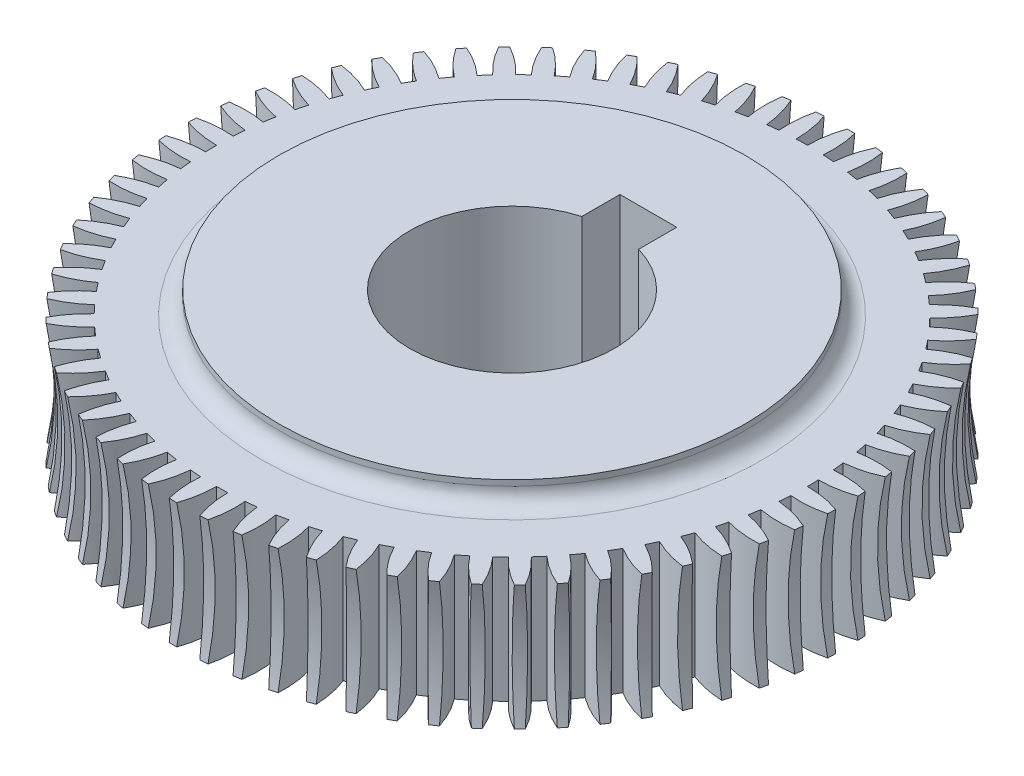
SolidWorks part; units mm, degrees
ref_plane "Front Plane" through (0, 0, 0) normal (0, 0, 1) x (1, 0, 0)
ref_plane "Top Plane" through (0, 0, 0) normal (0, 1, 0) x (1, 0, 0)
ref_plane "Right Plane" through (0, 0, 0) normal (1, 0, 0) x (0, 0, -1)
sketch "Sketch1" plane through (0, 0, 0) normal (0, 0, 1) x (1, 0, 0)
  line L5 (8.6582, -5.5) -> (37.6582, -5.5)
  line L7 (8.6582, 5.5) -> (37.6582, 5.5)
  line L9 (8.6582, 5.5) -> (8.6582, -5.5)
  arc A2 (37.6582, 5.5) -> (37.6582, -5.5) centre (67.1498, 0) ccw
  point P0 (0, 0)
  point P11 (8.6582, 0)
  dimension "D3" = 30
  dimension "D1" = 11
  dimension "D4" = 29
revolve "Revolve1" add sketch "Sketch1" angle 360 about L9
sketch "Sketch2" plane through (0, 5.5, 0) normal (0, 1, 0) x (1, 0, 0)
  circle A0 centre (8.6582, 0) radius 29 construction
  arc A3 (8.6582, -26) -> (9.6318, -25.9818) centre (8.6582, 0) ccw
  arc A4 (9.6318, -25.9818) -> (10.1451, -28.9619) centre (18.6318, -25.9659) ccw
  arc A5 (8.6582, -26) -> (8.1451, -28.9955) centre (-0.3418, -26) cw
  point P6 (9.1451, -25.9954)
  dimension "D1" = 52
  dimension "D3" = 9
  dimension "D4" = 9
  dimension "D7" = 3
  dimension "D2" = 1
  dimension "D5" = 2
  dimension "D6" = 1
extrude "Cut-Extrude1" cut sketch "Sketch2" against normal through all and the other way through all
pattern_circular "CirPattern1" count 68 over 360 about axis through (8.6582, 5.5, 0) along (0, 1, 0) of "Cut-Extrude1"
sketch "Sketch3" plane through (0, 5.5, 0) normal (0, 1, 0) x (1, 0, 0)
  line L1 (11.1582, 8.6458) -> (11.1582, 12)
  line L2 (6.1582, 8.6458) -> (6.1582, 12)
  line L6 (6.1582, 12) -> (11.1582, 12)
  arc A0 (31.7114, 12.023) -> (-14.3949, -12.023) centre (8.6582, 0) cw
  arc A1 (31.9325, 11.5892) -> (31.4822, 12.4526) centre (8.6582, 0) ccw construction
  arc A2 (-14.616, -11.5892) -> (-14.1657, -12.4526) centre (8.6582, 0) ccw construction
  circle A3 centre (8.6582, 0) radius 26
  arc A4 (6.1582, 8.6458) -> (11.1582, 8.6458) centre (8.6582, 0) ccw
  dimension "D1" = 18
extrude "Cut-Extrude2" cut sketch "Sketch3" against normal through all contours L2 A4 L1 L6
sketch "Sketch4" plane through (0, 5.5, 0) normal (0, 1, 0) x (1, 0, 0)
  line L0 (6.1582, 8.6458) -> (6.1582, 12)
  line L1 (6.1582, 12) -> (11.1582, 12)
  line L2 (11.1582, 12) -> (11.1582, 8.6458)
  circle A1 centre (8.6582, 0) radius 20.5
  arc A2 (6.1582, 8.6458) -> (11.1582, 8.6458) centre (8.6582, 0) ccw
  dimension "D1" = 41
extrude "Boss-Extrude1" add sketch "Sketch4" along normal blind 2
fillet "Fillet1" radius 1.5 1 edges at (8.6582, 5.5, -20.5)
mirror "Mirror7" about plane through (0, 0, 0) normal (0, 1, 0) of "Boss-Extrude1"
fillet "Fillet2" radius 1.5 1 edges at (8.6582, -5.5, 20.5)
